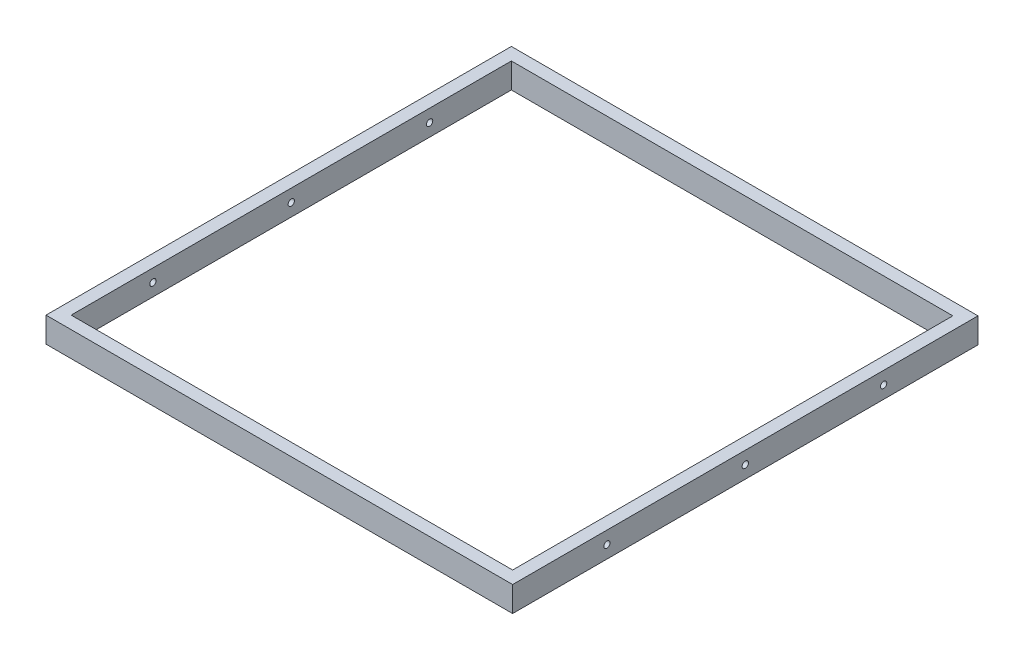
SolidWorks part; units mm, degrees
ref_plane "Front Plane" through (0, 0, 0) normal (0, 0, 1) x (1, 0, 0)
ref_plane "Top Plane" through (0, 0, 0) normal (0, 1, 0) x (1, 0, 0)
ref_plane "Right Plane" through (0, 0, 0) normal (1, 0, 0) x (0, 0, -1)
sketch "Sketch1" plane through (0, 0, 0) normal (0, 1, 0) x (1, 0, 0)
  line L0 (-185.5, 185) -> (185.5, 185)
  line L1 (-175.5, -175) -> (175.5, -175)
  line L2 (-175.5, -175) -> (-175.5, 175)
  line L3 (-175.5, 175) -> (175.5, 175)
  line L4 (175.5, -175) -> (175.5, 175)
  line L5 (-175.5, -175) -> (175.5, 175) construction
  line L6 (-175.5, 175) -> (175.5, -175) construction
  line L7 (185.5, -185) -> (185.5, 185)
  line L8 (-185.5, -185) -> (185.5, -185)
  line L9 (-185.5, -185) -> (-185.5, 185)
  point P0 (0, 0)
  dimension "D1" = 351
  dimension "D2" = 350
  dimension "D3" = 10
extrude "Boss-Extrude1" add sketch "Sketch1" along normal blind 20
sketch "Sketch2" plane through (185.5, 0, 0) normal (1, 0, 0) x (0, 0, -1)
  line L0 (0, 69.0819) -> (0, -86.3193) construction
  line L1 (-185, 20) -> (185, 20) construction
  circle A0 centre (0, 10) radius 2.5
  circle A1 centre (110, 10) radius 2.5
  circle A2 centre (-110, 10) radius 2.5
  dimension "D3" = 110
  dimension "D1" = 0
  dimension "D2" = 10
extrude "Cut-Extrude1" cut sketch "Sketch2" against normal up to surface (371 mm away) up to face at (-185.5, 10, 0)
